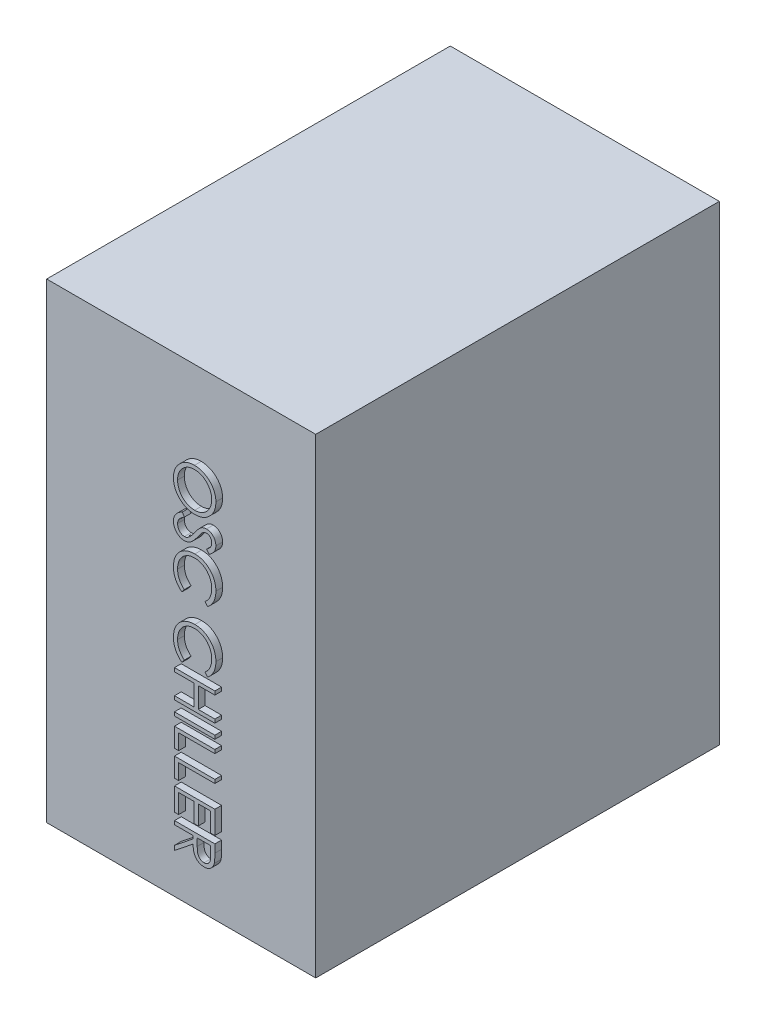
SolidWorks part; units mm, degrees
ref_plane "Front Plane" through (0, 0, 0) normal (0, 0, 1) x (1, 0, 0)
ref_plane "Top Plane" through (0, 0, 0) normal (0, 1, 0) x (1, 0, 0)
ref_plane "Right Plane" through (0, 0, 0) normal (1, 0, 0) x (0, 0, -1)
sketch "Sketch1" plane through (0, 0, 0) normal (0, 0, 1) x (1, 0, 0)
  line L1 (0, 0) -> (-200, 0)
  line L2 (0, 0) -> (0, -350)
  line L3 (0, -350) -> (-200, -350)
  line L4 (-200, 0) -> (-200, -350)
  dimension "D1" = 200
  dimension "D2" = 350
extrude "Boss-Extrude1" add sketch "Sketch1" along normal blind 300
sketch "Sketch2" plane through (0, 0, 300) normal (0, 0, 1) x (1, 0, 0)
  line L0 (-100, 0) -> (-100, -350) construction
  line L1 (0, 0) -> (-200, 0) construction
  line L2 (-200, -350) -> (0, -350) construction
  text T0 "     OSC CHILLER" font "Century Gothic" height 30
extrude "Boss-Extrude2" add sketch "Sketch2" along normal blind 5
